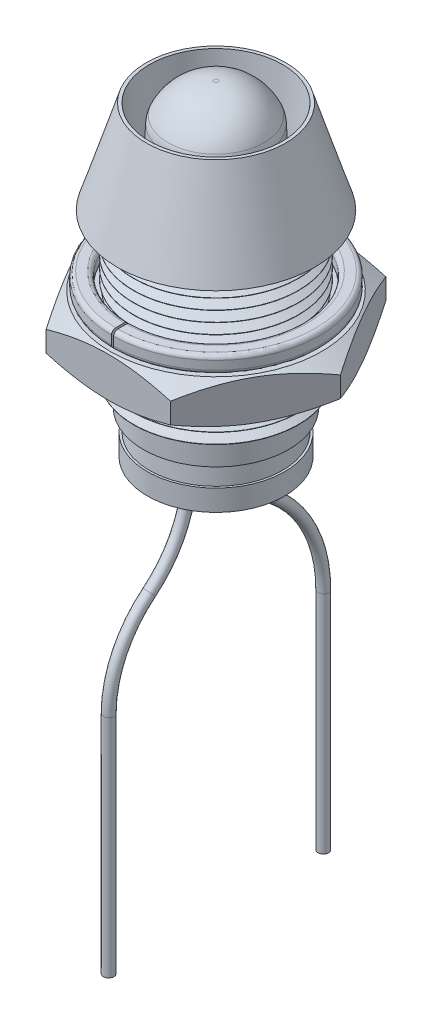
SolidWorks part; units mm, degrees
other "Washer Lock"
other "Nut"
other "Tip"
other "Wire LED"
other "LED Light"
other "Plastic Insert"
material "Plain Carbon Steel"
ref_plane "Front Plane" through (0, 0, 0) normal (0, 0, 1) x (1, 0, 0)
ref_plane "Top Plane" through (0, 0, 0) normal (0, 1, 0) x (1, 0, 0)
ref_plane "Right Plane" through (0, 0, 0) normal (1, 0, 0) x (0, 0, -1)
sketch "Sketch1" plane through (0, 0, 0) normal (0, 0, 1) x (1, 0, 0)
  line L0 (0, 0) -> (0, 12.5)
  line L1 (0, 0) -> (3.44, 0)
  line L2 (3.9, 1) -> (3.9, 8.1)
  line L3 (0, 12.5) -> (3.3, 12.5)
  line L4 (3.9, 8.1) -> (4.68, 8.1)
  line L5 (4.68, 8.1) -> (3.3, 12.5)
  line L6 (3.44, 0) -> (3.44, 1)
  line L7 (3.44, 1) -> (3.9, 1)
  dimension "D1" = 12.5
  dimension "D2" = 3.9
  dimension "D3" = 3.3
  dimension "D4" = 4.68
  dimension "D5" = 4.4
  dimension "D6" = 3.44
  dimension "D7" = 8.1
  dimension "D8" = 1
revolve "Revolve1" add sketch "Sketch1" angle 360 about L0
sketch "Sketch6" plane through (0, 0, 0) normal (0, 0, 1) x (1, 0, 0)
  line L0 (0, 0) -> (0, 12.5)
  line L1 (3.3, 12.5) -> (-3.3, 12.5) construction
  line L2 (0, 0) -> (3.05, 0)
  line L3 (3.05, 0) -> (3.05, 5.8)
  line L4 (3.05, 5.8) -> (2.65, 5.8)
  line L5 (2.65, 5.8) -> (3.15, 12.5)
  line L6 (3.15, 12.5) -> (0, 12.5)
  line L7 (2.65, 5.8) -> (0, 5.8) construction
  dimension "D1" = 3.05
  dimension "D2" = 5.8
  dimension "D3" = 3.15
  dimension "D4" = 2.65
revolve "Cut-Revolve2" cut sketch "Sketch6" angle 360 about L0
sketch "Sketch5" plane through (0, 0, 0) normal (0, 0, 1) x (1, 0, 0)
  line L0 (0, 0) -> (0, 1) construction
  line L1 (-3.44, 1) -> (3.44, 1) construction
  line L2 (0, 1) -> (3.48, 1) construction
  line L3 (3.48, 1) -> (3.913, 1) construction
  line L4 (3.913, 1) -> (4.413, 1) construction
  line L5 (4.413, 1.25) -> (4.413, 0.75)
  line L6 (3.913, 1.25) -> (3.913, 0.75) construction
  line L7 (4.413, 1.25) -> (3.913, 1.25)
  line L8 (3.913, 1.25) -> (3.48, 1)
  line L9 (3.48, 1) -> (3.913, 0.75)
  line L10 (3.913, 0.75) -> (4.413, 0.75)
  dimension "D1" = 0.5
  dimension "D2" = 60
  dimension "D3" = 3.48
revolve "Cut-Revolve1" cut sketch "Sketch5" angle 360 about L0
pattern_linear "LPattern1" count 14 spacing 0.5 along (0, 1, 0) of "Cut-Revolve1"
ref_plane "GAP DISTANCE" through (0, 4.8, 0) normal (0, -1, 0) x (-1, 0, 0)
sketch "Sketch7" plane through (0, 4.8, 0) normal (0, -1, 0) x (-1, 0, 0)
  line L1 (-5.889, 0) -> (-2.9445, -5.1)
  line L2 (-2.9445, -5.1) -> (2.9445, -5.1)
  line L3 (2.9445, -5.1) -> (5.889, 0)
  line L4 (5.889, 0) -> (2.9445, 5.1)
  line L5 (2.9445, 5.1) -> (-2.9445, 5.1)
  line L6 (-2.9445, 5.1) -> (-5.889, 0)
  circle A0 centre (0, 0) radius 5.1 construction
  circle A1 centre (0, 0) radius 3.65
  dimension "D1" = 10.2
  dimension "D2" = 7.3
extrude "Boss-Extrude1" add sketch "Sketch7" along normal blind 2 separate body
sketch "Sketch8" plane through (0, 0, 0) normal (0, 0, 1) x (1, 0, 0)
  line L0 (0, 0) -> (0, 2.8) construction
  line L1 (2.9445, 2.8) -> (-2.9445, 2.8) construction
  line L2 (0, 2.8) -> (0, 4.8) construction
  line L3 (2.9445, 4.8) -> (-2.9445, 4.8) construction
  line L4 (0, 4.8) -> (5, 4.8) construction
  line L5 (5.889, 4.8) -> (2.9445, 4.8) construction
  line L6 (5, 4.8) -> (5, 2.8) construction
  line L7 (5.889, 2.8) -> (2.9445, 2.8) construction
  line L8 (5, 2.8) -> (0, 2.8) construction
  line L9 (5, 4.8) -> (5.889, 4.8)
  line L10 (5.889, 4.8) -> (5.889, 4.2868)
  line L11 (5.889, 2.8) -> (5.889, 4.8) construction
  line L12 (5.889, 4.2868) -> (5, 4.8)
  line L13 (5, 2.8) -> (5.889, 2.8)
  line L14 (5.889, 2.8) -> (5.889, 3.3132)
  line L15 (5.889, 3.3132) -> (5, 2.8)
  dimension "D1" = 30
  dimension "D2" = 30
  dimension "D3" = 5
revolve "Cut-Revolve3" cut sketch "Sketch8" angle 360 about L2
sketch "Sketch9" plane through (0, 4.8, 0) normal (0, 1, 0) x (1, 0, 0)
  circle A0 centre (0, 0) radius 4.9
  circle A1 centre (0, 0) radius 4.1
  dimension "D1" = 9.8
  dimension "D2" = 0.8
extrude "Boss-Extrude2" add sketch "Sketch9" along normal blind 0.8 separate body
fillet "Fillet1" radius 0.2 4 edges at (0, 4.8, 4.1) (0, 5.6, 4.1) (0, 4.8, 4.9) (0, 5.6, 4.9)
sketch "Sketch10" plane through (0, 5.6, 0) normal (0, 1, 0) x (1, 0, 0)
  line L0 (0, 0) -> (0, -3.5) construction
  line L2 (-0.05, -3.5) -> (0.05, -3.5)
  line L3 (-0.05, -3.5) -> (-0.05, -5.5)
  line L4 (-0.05, -5.5) -> (0.05, -5.5)
  line L5 (0.05, -3.5) -> (0.05, -5.5)
  dimension "D1" = 0.1
  dimension "D2" = 3.5
  dimension "D3" = 2
extrude "Cut-Extrude4" cut sketch "Sketch10" against normal up to surface (0.8 mm away)
sketch "Sketch11" plane through (0, 0, 0) normal (0, 0, 1) x (1, 0, 0)
  line L0 (0, 4.8) -> (0, -2)
  line L1 (0, -2) -> (3.25, -2)
  line L2 (0, 4.8) -> (2.8, 4.8)
  line L4 (3.25, -2) -> (3.25, -1)
  line L5 (3.25, -1) -> (3.15, -1)
  line L6 (3.15, -1) -> (2.8, 4.8)
  line L7 (0, 4.8) -> (0, 12.5) construction
  line L8 (3.3, 12.5) -> (-3.3, 12.5) construction
  dimension "D1" = 0.1
  dimension "D2" = 3.25
  dimension "D3" = 2.8
  dimension "D4" = 6.8
  dimension "D5" = 1
  dimension "D6" = 14.5
revolve "Revolve2" add sketch "Sketch11" angle 360 about L7
sketch "Sketch12" plane through (0, 4.8, 0) normal (0, 1, 0) x (1, 0, 0)
  circle A0 centre (0, 0) radius 2.45
  dimension "D1" = 4.9
extrude "Cut-Extrude5" cut sketch "Sketch12" against normal offset from surface (4.8 mm away) 2 up to face at (0, -2, -3.25)
sketch "Sketch13" plane through (0, 0, 0) normal (0, 1, 0) x (1, 0, 0)
  line L0 (0, 1.27) -> (0, -1.27) construction
  line L2 (-0.4, 1.67) -> (0.4, 1.67)
  line L3 (-0.4, 1.67) -> (-0.4, 0.87)
  line L4 (-0.4, 0.87) -> (0.4, 0.87)
  line L5 (0.4, 1.67) -> (0.4, 0.87)
  line L6 (-0.4, 1.67) -> (0.4, 0.87) construction
  line L7 (-0.4, 0.87) -> (0.4, 1.67) construction
  line L8 (-0.4, -0.87) -> (0.4, -0.87)
  line L9 (-0.4, -0.87) -> (-0.4, -1.67)
  line L10 (-0.4, -1.67) -> (0.4, -1.67)
  line L11 (0.4, -0.87) -> (0.4, -1.67)
  line L12 (-0.4, -0.87) -> (0.4, -1.67) construction
  line L13 (-0.4, -1.67) -> (0.4, -0.87) construction
  dimension "D1" = 2.54
  dimension "D2" = 0.8
extrude "Cut-Extrude6" cut sketch "Sketch13" against normal up to surface (2 mm away) up to face at (0, -2, -3.25)
sketch "Sketch14" plane through (0, -2, 0) normal (0, -1, 0) x (1, 0, 0)
  line L0 (0, 1.67) -> (0, 0.87) construction
  line L1 (-0.4, 1.67) -> (0.4, 1.67) construction
  line L2 (0.4, 0.87) -> (-0.4, 0.87) construction
  line L3 (0, -0.87) -> (0, -1.67) construction
  line L4 (-0.4, -0.87) -> (0.4, -0.87) construction
  line L5 (0.4, -1.67) -> (-0.4, -1.67) construction
  circle A0 centre (0, -1.27) radius 0.75
  circle A1 centre (0, 1.27) radius 0.75
  dimension "D1" = 1.5
extrude "Cut-Extrude7" cut sketch "Sketch14" against normal blind 0.1
sketch "Sketch21" plane through (0, -2, 0) normal (0, -1, 0) x (1, 0, 0)
  line L0 (0, 0) -> (0, 2.2) construction
  line L1 (0, 0) -> (0, -3) construction
  line L2 (-1.25, -3) -> (1.25, -3) construction
  line L3 (-1.25, 2.2) -> (1.25, 2.2) construction
  circle A0 centre (0, 0) radius 3.25 construction
  text T0 "A" font "Calibri" height 0.8
  text T1 "C" font "Calibri" height 0.8
  dimension "D1" = 3
  dimension "D2" = 2.2
extrude "Cut-Extrude9" cut sketch "Sketch21" against normal blind 0.01
sketch "Sketch15" plane through (0, 0, 0) normal (0, 0, 1) x (1, 0, 0)
  line L0 (0, 0) -> (0, 4.8) construction
  line L1 (2.8, 4.8) -> (-2.8, 4.8) construction
  line L2 (0, 4.8) -> (0, 13.4)
  line L3 (0, 4.8) -> (2.8, 4.8)
  line L4 (2.8, 4.8) -> (2.8, 6)
  line L5 (2.8, 6) -> (2.49, 6)
  line L6 (2.49, 6) -> (2.49, 6.3)
  line L8 (0.1, 13.4) -> (0, 13.4)
  line L9 (2.49, 6.3) -> (2.49, 11.8) construction
  line L10 (2.49, 11.8) -> (2.49, 13.4) construction
  line L11 (2.49, 13.4) -> (0.1, 13.4) construction
  line L12 (2.49, 11.8) -> (2.35, 11.8) construction
  line L13 (2.49, 6) -> (0, 6) construction
  line L14 (2.35, 11.8) -> (0, 11.8) construction
  arc A0 (2.49, 6.3) -> (2.3582, 11.6364) centre (-105.6157, 6.3) ccw
  arc A1 (0.1, 13.4) -> (2.2707, 11.9988) centre (0.1, 11.018) cw
  arc A2 (2.2707, 11.9988) -> (2.3582, 11.6364) centre (1.3594, 11.587) cw
  dimension "D1" = 2.49
  dimension "D7" = 0.1
  dimension "D9" = 1
  dimension "D2" = 2.8
  dimension "D3" = 1.2
  dimension "D4" = 8.6
  dimension "D5" = 2.35
  dimension "D6" = 1.5
  dimension "D8" = 7
revolve "Revolve3" add sketch "Sketch15" angle 360 about L2
sketch "Sketch17" plane through (0, 6, 0) normal (0, 1, 0) x (1, 0, 0)
  line L0 (0, 0) -> (0, 2.52) construction
  line L1 (-1.2205, 2.52) -> (1.2205, 2.52)
  circle A0 centre (0, 0) radius 2.8 construction
  arc A1 (1.2205, 2.52) -> (-1.2205, 2.52) centre (0, 0) ccw
  dimension "D1" = 2.52
extrude "Cut-Extrude8" cut sketch "Sketch17" against normal up to surface (1.2 mm away) up to face at (0, 4.8, -2.8)
sketch "Sketch Wire Path" plane through (0, 0, 0) normal (1, 0, 0) x (0, 0, -1)
  line L0 (0, 0) -> (0, 4.8) construction
  line L1 (-1.27, -2) -> (1.27, -2) construction
  line L2 (-2.8, 4.8) -> (2.52, 4.8) construction
  line L3 (0, 4.8) -> (0, 6) construction
  line L4 (2.52, 6) -> (-2.8, 6) construction
  line L5 (-1.27, 5.4) -> (0, 5.4)
  line L6 (-1.27, 5.4) -> (-1.27, -2)
  line L7 (1.27, 5.4) -> (1.27, -2)
  line L8 (-1.27, -2) -> (-1.27, -6) construction
  line L9 (-1.27, -6) -> (-3.175, -6) construction
  line L10 (-3.175, -6) -> (-5.08, -6) construction
  line L11 (-5.08, -6) -> (-5.08, -10) construction
  line L12 (1.27, -2) -> (1.27, -5) construction
  line L13 (1.27, -5) -> (2.6987, -5) construction
  line L14 (2.6987, -5) -> (5.08, -5) construction
  line L15 (5.08, -5) -> (5.08, -10) construction
  line L16 (-5.08, -10) -> (-5.08, -20.6705)
  line L17 (5.08, -10) -> (5.08, -20.6705)
  line L18 (0, 0) -> (0, -20.6705) construction
  line L19 (-5.08, -20.6705) -> (0, -20.6705) construction
  line L20 (0, -20.6705) -> (5.08, -20.6705) construction
  line L21 (0, 5.4) -> (1.27, 5.4)
  line L22 (-3.25, -2) -> (3.25, -2) construction
  arc A0 (-1.27, -2) -> (-3.175, -6) centre (-6.422, -2) cw
  arc A1 (-3.175, -6) -> (-5.08, -10) centre (0.072, -10) ccw
  arc A2 (1.27, -2) -> (2.6987, -5) centre (5.134, -2) ccw
  arc A3 (2.6987, -5) -> (5.08, -10) centre (-1.36, -10) cw
  point P23 (0, -2)
  dimension "D2" = 57
  dimension "D3" = 8
  dimension "D1" = 2.54
  dimension "D4" = 5.08
  dimension "D5" = 5.08
  dimension "D7" = 8
  dimension "D8" = 4
  dimension "D9" = 5
sketch "Sketch Wire Profile" plane through (0, 0, 0) normal (0, 0, 1) x (1, 0, 0)
  line L0 (0, 4.8) -> (0, 6) construction
  circle A0 centre (0, 5.4) radius 0.25
  dimension "D1" = 0.5
sweep "ADJUST LED WIRES" add profiles "Sketch Wire Profile" path "Sketch Wire Path"
